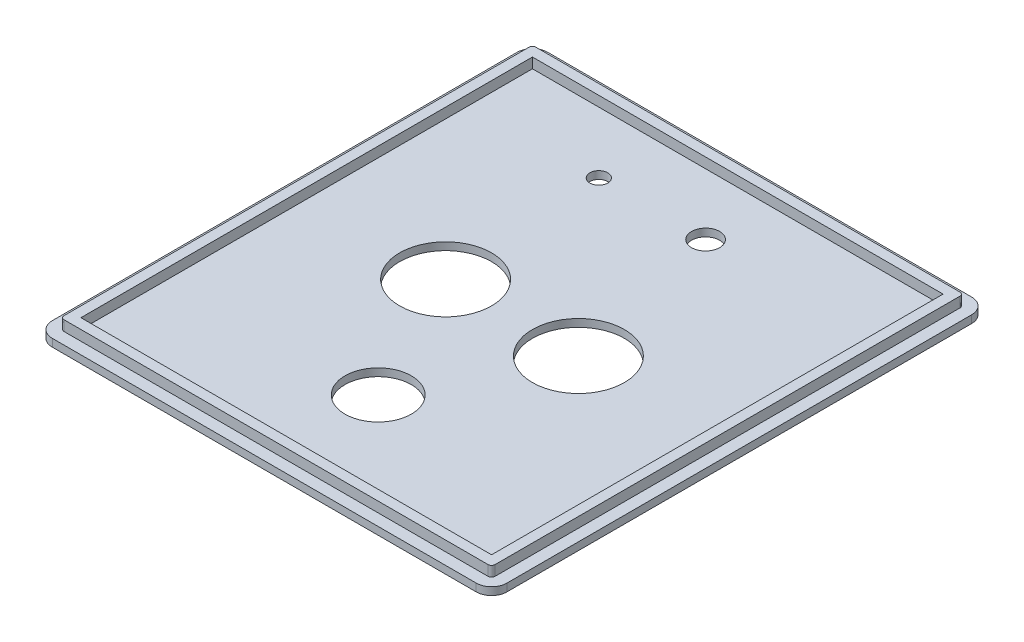
SolidWorks part; units mm, degrees
ref_plane "Front Plane" through (0, 0, 0) normal (0, 0, 1) x (1, 0, 0)
ref_plane "Top Plane" through (0, 0, 0) normal (0, 1, 0) x (1, 0, 0)
ref_plane "Right Plane" through (0, 0, 0) normal (1, 0, 0) x (0, 0, -1)
sketch "Sketch1" plane through (0, 0, 0) normal (0, 1, 0) x (1, 0, 0)
  line L1 (3, 0) -> (86, 0)
  line L2 (0, 3) -> (0, 94)
  line L3 (3, 97) -> (86, 97)
  line L4 (89, 3) -> (89, 94)
  arc A0 (0, 94) -> (3, 97) centre (3, 94) cw
  arc A1 (3, 0) -> (0, 3) centre (3, 3) cw
  arc A2 (86, 0) -> (89, 3) centre (86, 3) ccw
  arc A3 (86, 97) -> (89, 94) centre (86, 94) cw
  point P7 (0, 97)
  point P10 (0, 0)
  point P13 (89, 0)
  dimension "D3" = 3
  dimension "D4" = 3
  dimension "D1" = 89
  dimension "D2" = 97
extrude "Boss-Extrude1" add sketch "Sketch1" along normal blind 1.5
sketch "Sketch2" plane through (0, 1.5, 0) normal (0, 1, 0) x (1, 0, 0)
  line L2 (2.3, 94) -> (2.3, 3)
  line L3 (2.3, 94) -> (2.3, 3)
  line L5 (86, 94.7) -> (3, 94.7)
  line L6 (86, 94.7) -> (3, 94.7)
  line L8 (86.7, 3) -> (86.7, 94)
  line L9 (86.7, 3) -> (86.7, 94)
  line L11 (3, 2.3) -> (86, 2.3)
  line L12 (3, 2.3) -> (86, 2.3)
  arc A2 (3, 94.7) -> (2.3, 94) centre (3, 94) ccw
  arc A3 (3, 94.7) -> (2.3, 94) centre (3, 94) ccw
  arc A5 (86.7, 94) -> (86, 94.7) centre (86, 94) ccw
  arc A6 (86.7, 94) -> (86, 94.7) centre (86, 94) ccw
  arc A8 (86, 2.3) -> (86.7, 3) centre (86, 3) ccw
  arc A9 (86, 2.3) -> (86.7, 3) centre (86, 3) ccw
  arc A11 (2.3, 3) -> (3, 2.3) centre (3, 3) ccw
  arc A12 (2.3, 3) -> (3, 2.3) centre (3, 3) ccw
  dimension "D1" = 2.3
  dimension "D2" = 2.3
  dimension "D3" = 2.3
  dimension "D4" = 2.3
  dimension "D5" = 2.3
  dimension "D6" = 2.3
  dimension "D7" = 2.3
  dimension "D8" = 2.3
extrude "Boss-Extrude2" add sketch "Sketch2" along normal blind 2
sketch "Sketch3" plane through (0, 3.5, 0) normal (0, 1, 0) x (1, 0, 0)
  line L1 (2.3, 94) -> (2.3, 3) construction
  line L2 (4.3, 92.7) -> (84.7, 92.7)
  line L3 (4.3, 92.7) -> (4.3, 4.3)
  line L4 (4.3, 4.3) -> (84.7, 4.3)
  line L5 (84.7, 92.7) -> (84.7, 4.3)
  line L6 (86.7, 3) -> (86.7, 94) construction
  line L7 (86, 94.7) -> (3, 94.7) construction
  line L8 (3, 2.3) -> (86, 2.3) construction
  dimension "D1" = 2
  dimension "D2" = 2
  dimension "D3" = 2
  dimension "D4" = 2
extrude "Cut-Extrude1" cut sketch "Sketch3" against normal blind 2
sketch "Sketch4" plane through (0, 1.5, 0) normal (0, 1, 0) x (1, 0, 0)
  line L0 (2.3, 94) -> (2.3, 3) construction
  line L3 (3, 2.3) -> (86, 2.3) construction
  circle A0 centre (31.5, 48.5) radius 9
  circle A1 centre (57.5, 48.5) radius 9
  point P4 (0, 0)
  dimension "D1" = 18
  dimension "D2" = 26
  dimension "D3" = 29.2
  dimension "D4" = 46.2
extrude "Cut-Extrude2" cut sketch "Sketch4" against normal blind 2
sketch "Sketch5" plane through (0, 1.5, 0) normal (0, 1, 0) x (1, 0, 0)
  line L0 (86, 94.7) -> (3, 94.7) construction
  line L1 (86.7, 3) -> (86.7, 94) construction
  line L2 (2.3, 94) -> (2.3, 3) construction
  circle A0 centre (29.3, 80.7) radius 1.75
  circle A1 centre (50.2, 80.7) radius 2.75
  point P4 (0, 0)
  dimension "D1" = 3.5
  dimension "D2" = 5.5
  dimension "D3" = 14
  dimension "D4" = 36.5
  dimension "D5" = 27
extrude "Cut-Extrude3" cut sketch "Sketch5" against normal blind 2
sketch "Sketch6" plane through (0, 1.5, 0) normal (0, 1, 0) x (1, 0, 0)
  line L0 (86.7, 3) -> (86.7, 94) construction
  line L2 (3, 2.3) -> (86, 2.3) construction
  circle A0 centre (44.5, 22.3) radius 6.5
  dimension "D1" = 13
  dimension "D2" = 42.2
  dimension "D3" = 20
extrude "Cut-Extrude4" cut sketch "Sketch6" against normal blind 2
